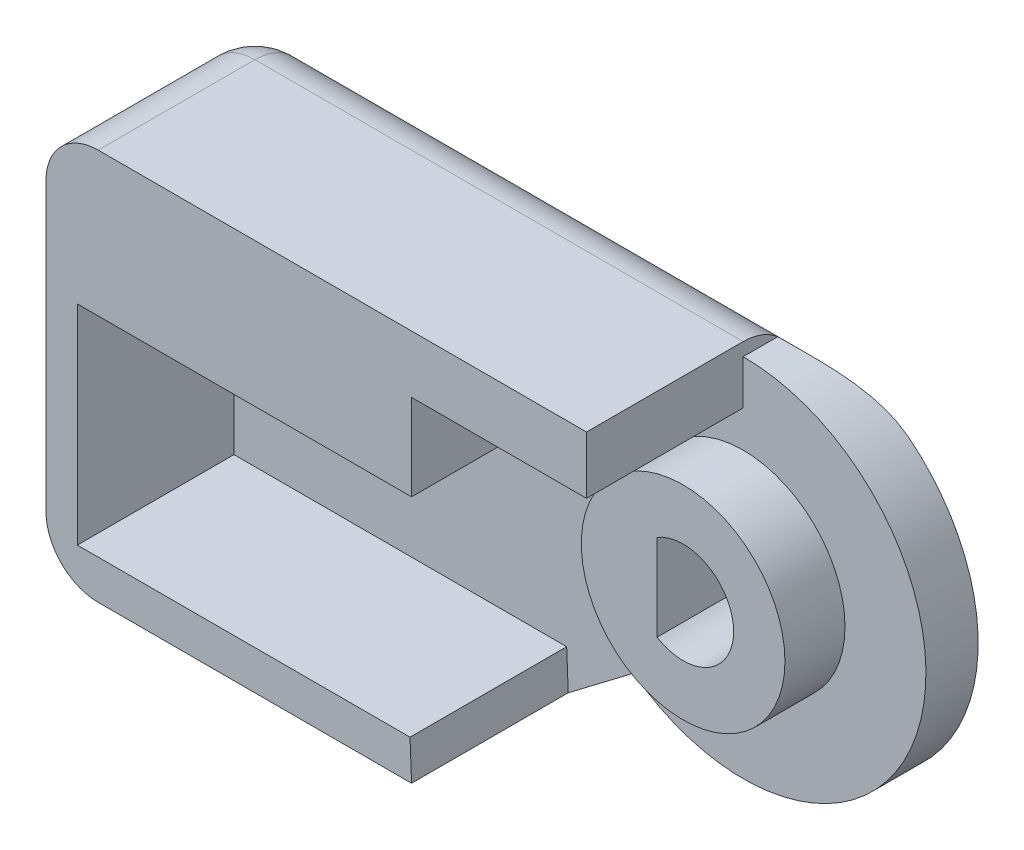
SolidWorks part; units mm, degrees
ref_plane "Front Plane" through (0, 0, 0) normal (0, 0, 1) x (1, 0, 0)
ref_plane "Top Plane" through (0, 0, 0) normal (0, 1, 0) x (1, 0, 0)
ref_plane "Right Plane" through (0, 0, 0) normal (1, 0, 0) x (0, 0, -1)
sketch "Sketch2" plane through (0, 0, 0) normal (0, 0, 1) x (1, 0, 0)
  line L1 (-2.5, 7.5) -> (-20.7, 7.5)
  line L2 (-20.7, 7.5) -> (-20.7, -7.5)
  line L3 (-20.7, -7.5) -> (-6.7, -7.5)
  line L4 (-6.7, -7.5) -> (-4.2, -5.6)
  line L5 (-2.5, 7.5) -> (0, 7.5)
  line L7 (0, 7) -> (0, 7.5)
  arc A1 (-4.2, -5.6) -> (7, 0) centre (0, 0) ccw
  arc A2 (7, 0) -> (0, 7) centre (0, 0) ccw
  dimension "D1" = 7
  dimension "D3" = 15
  dimension "D4" = 7.5
  dimension "D5" = 15
  dimension "D7" = 2.5
  dimension "D8" = 14
extrude "Boss-Extrude1" add sketch "Sketch2" along normal blind 2 contours A1 A2 L7 L5 L1 L2 L3 L4
sketch "Sketch4" plane through (0, 0, 2) normal (0, 0, 1) x (1, 0, 0)
  line L0 (-20.7, -7.5) -> (-20.7, 7.5)
  line L3 (-6.7, 2) -> (-19.5, 2)
  line L4 (-19.5, 2) -> (-19.5, -6)
  line L5 (-20.7, -7.5) -> (-6.7, -7.5) construction
  line L6 (-19.2926, -7.5) -> (-20.7, -7.5)
  line L7 (-19.2926, -7.5) -> (-6.7, -7.5)
  line L8 (-6.7, -7.5) -> (-6.7591, -6)
  line L9 (-6.7591, -6) -> (-19.5, -6)
  line L10 (-20.7, 7.5) -> (-0.7, 7.5)
  line L11 (-20.7, 7.5) -> (0, 7.5) construction
  line L13 (-6.7, 2) -> (-6.7, 5.3)
  line L14 (-6.7, 5.3) -> (-0.7, 5.3)
  line L15 (-0.7, 7.5) -> (0, 7.5)
  line L16 (-0.7, 5.3) -> (0, 5.3)
  line L19 (0, 5.3) -> (0, 7.5)
  dimension "D1" = 2
  dimension "D2" = 1.2
  dimension "D3" = 1.5
  dimension "D5" = 2.2
  dimension "D6" = 14
extrude "Boss-Extrude2" add sketch "Sketch4" along normal blind 6
ref_point "Point1"
sketch "Sketch22" plane through (0, 0, 2) normal (0, 0, 1) x (1, 0, 0)
  line L0 (0, 5.3) -> (-14, 5.3) construction
  line L1 (0, 4) -> (-14, 4) construction
  line L2 (-14, 4) -> (-14, 5.3) construction
  circle A0 centre (0, 0) radius 5.3 construction
  circle A1 centre (0, 0) radius 4 construction
  dimension "D1" = 14
sketch "Sketch24" plane through (0, 0, 2) normal (0, 0, 1) x (1, 0, 0)
  circle A0 centre (0, 0) radius 3.9
  dimension "D1" = 7.8
extrude "Boss-Extrude5" add sketch "Sketch24" along normal blind 2.3
sketch "Sketch29" plane through (-6.7, 0, 0) normal (1, 0, 0) x (0, 0, -1)
  line L0 (-1.9279, 3.9758) -> (-8, 3.9758) construction
  line L1 (-8, 2) -> (-8, 5.3) construction
sketch "Sketch30" plane through (-6.7, 0, 0) normal (1, 0, 0) x (0, 0, -1)
  line L0 (-4.4659, 3.9758) -> (-4.4659, 5.3)
  line L1 (-4.4659, 3.9758) -> (-2.0573, 3.9758)
  line L2 (-4.4659, 5.3) -> (-2.0573, 5.3)
  line L3 (-2.0573, 3.9758) -> (-2.0573, 5.3)
  line L4 (-1.9279, 3.9758) -> (-8, 3.9758) construction
  line L5 (-8, 5.3) -> (-2, 5.3) construction
extrude "Cut-Extrude12" cut sketch "Sketch30" against normal blind 8
ref_plane "Plane1" through (0, 0, 8) normal (0, 0, 1) x (1, 0, 0)
fillet "Fillet2" radius 2 5 edges at (-20.7, 0, 0) (-20.7, 7.5, 4) (-13.7, -7.5, 0) (-10.35, 7.5, 0) (-20.7, -7.5, 4)
sketch "Sketch8" plane through (0, 0, 2) normal (0, 0, 1) x (1, 0, 0)
  circle A1 centre (0, 0) radius 3.8
  circle A2 centre (0, 0) radius 2.5
sketch "Sketch28" plane through (0, 0, 4.3) normal (0, 0, 1) x (1, 0, 0)
  line L0 (-1, 1.6563) -> (-1, -1.6563)
  arc A0 (-1, -1.6563) -> (-1, 1.6563) centre (0, 0) ccw
  dimension "D1" = 1
extrude "Cut-Extrude11" cut sketch "Sketch28" against normal blind 10
